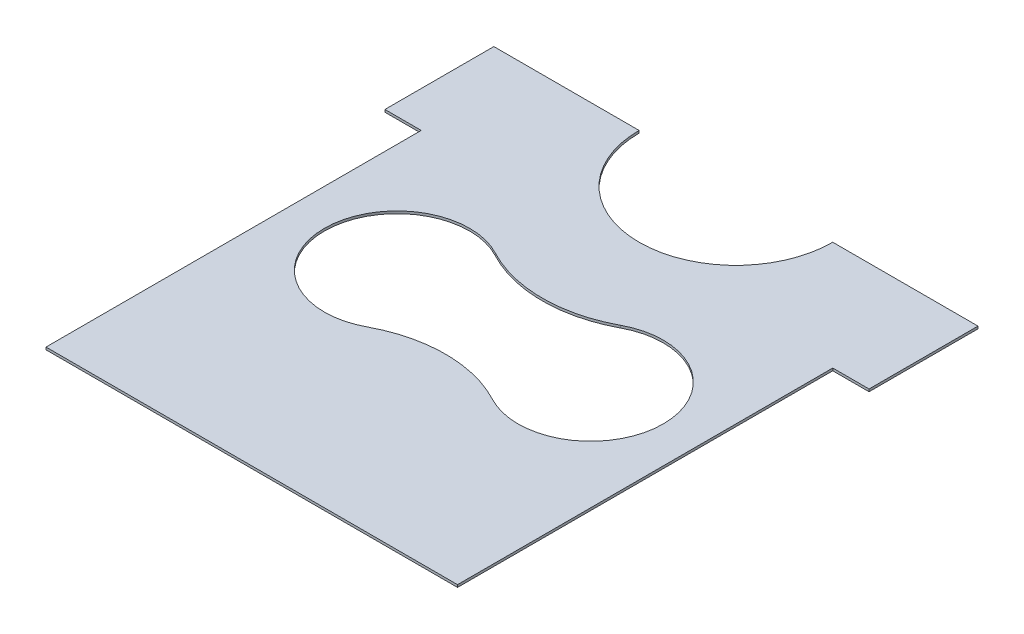
SolidWorks part; units mm, degrees
ref_plane "Face" through (0, 0, 0) normal (0, 0, 1) x (1, 0, 0)
ref_plane "Dessus" through (0, 0, 0) normal (0, 1, 0) x (1, 0, 0)
ref_plane "Droite" through (0, 0, 0) normal (1, 0, 0) x (0, 0, -1)
sketch "Esquisse1" plane through (0, 0, 0) normal (0, 1, 0) x (1, 0, 0)
  line L0 (0, 0) -> (0, 2000) construction
  line L1 (0, 2000) -> (1500, 2000) construction
  line L2 (1500, 2000) -> (1500, 0) construction
  line L3 (1500, 0) -> (0, 0) construction
  line L4 (2350, 0) -> (650, 0)
  line L5 (650, 0) -> (650, 1550)
  line L6 (650, 1550) -> (500, 1550)
  line L7 (500, 1550) -> (500, 2000)
  line L8 (500, 2000) -> (1100, 2000)
  line L9 (1500, 1000) -> (0, 1000) construction
  line L11 (2500, 2000) -> (1900, 2000)
  line L12 (2500, 1550) -> (2500, 2000)
  line L13 (2350, 1550) -> (2500, 1550)
  line L14 (2350, 0) -> (2350, 1550)
  arc A0 (1100, 2000) -> (1900, 2000) centre (1500, 2000) ccw
  arc A1 (1241.1765, 1264.7059) -> (1241.1765, 735.2941) centre (1100, 1000) ccw
  arc A2 (1241.1765, 1264.7059) -> (1758.8235, 1264.7059) centre (1500, 1750) ccw
  arc A3 (1241.1765, 735.2941) -> (1758.8235, 735.2941) centre (1500, 250) cw
  arc A4 (1758.8235, 1264.7059) -> (1758.8235, 735.2941) centre (1900, 1000) cw
  point P15 (800, 1000)
  dimension "D6" = 400
  dimension "D7" = 300
  dimension "D9" = 550
  dimension "D1" = 2000
  dimension "D2" = 1500
  dimension "D3" = 500
  dimension "D4" = 450
  dimension "D5" = 150
  dimension "D8" = 800
extrude "Extrusion1" add sketch "Esquisse1" along normal blind 10
